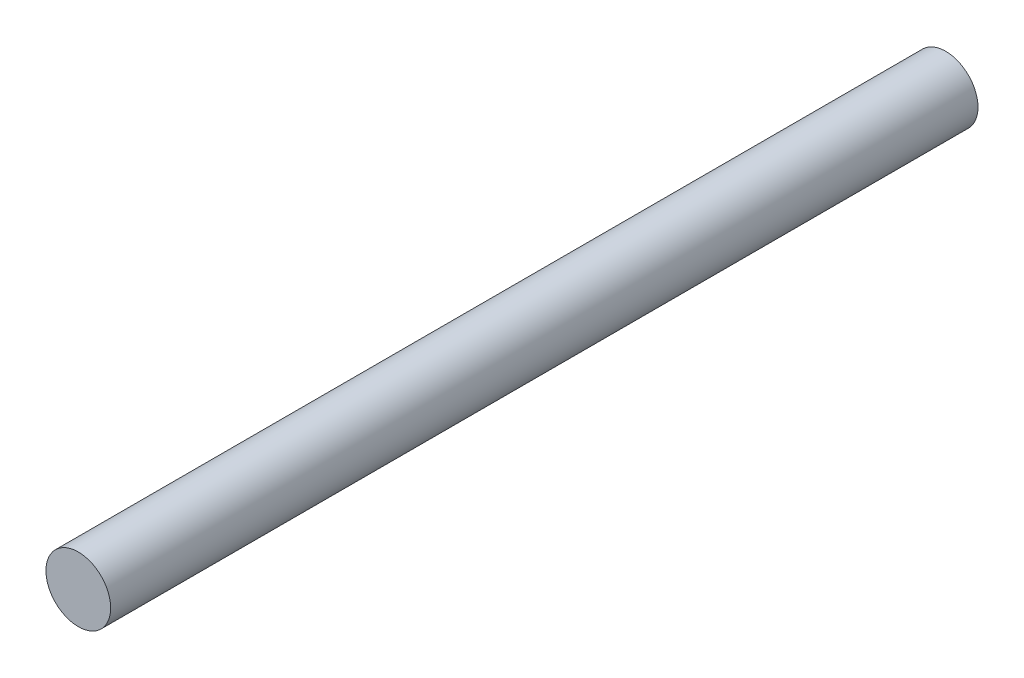
SolidWorks part; units mm, degrees
material "201 Annealed Stainless Steel (SS)"
ref_plane "Front Plane" through (0, 0, 0) normal (0, 0, 1) x (1, 0, 0)
ref_plane "Top Plane" through (0, 0, 0) normal (0, 1, 0) x (1, 0, 0)
ref_plane "Right Plane" through (0, 0, 0) normal (1, 0, 0) x (0, 0, -1)
sketch "Sketch1" plane through (0, 0, 0) normal (0, 0, 1) x (1, 0, 0)
  circle A0 centre (0, 0) radius 3.175
  dimension "D1" = 6.35
extrude "Boss-Extrude1" add sketch "Sketch1" along normal blind 85.09
